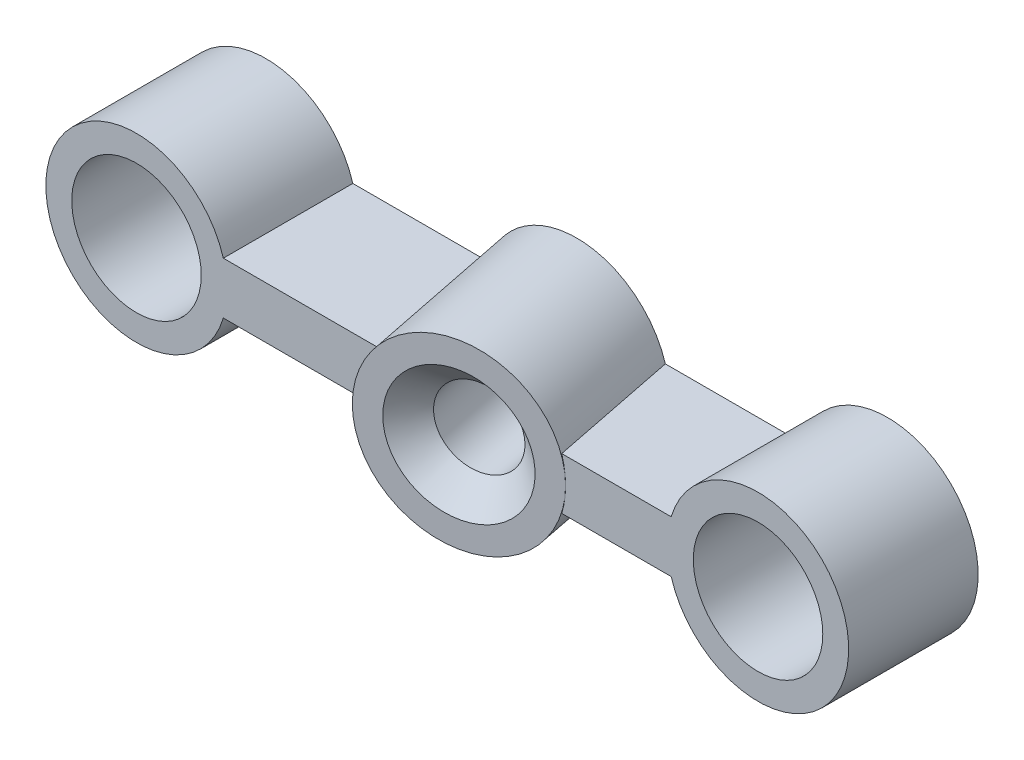
SolidWorks part; units mm, degrees
ref_plane "Front Plane" through (0, 0, 0) normal (0, 0, 1) x (1, 0, 0)
ref_plane "Top Plane" through (0, 0, 0) normal (0, 1, 0) x (1, 0, 0)
ref_plane "Right Plane" through (0, 0, 0) normal (1, 0, 0) x (0, 0, -1)
sketch "Sketch1" plane through (0, 0, 0) normal (0, 0, 1) x (1, 0, 0)
  line L0 (-20.6459, 1) -> (-3.3541, 1)
  line L1 (-3.3541, -1) -> (-20.6459, -1)
  circle A0 centre (0, 0) radius 2.5
  circle A1 centre (-24, 0) radius 2.5
  arc A2 (-20.6459, 1) -> (-20.6459, -1) centre (-24, 0) ccw
  arc A3 (-3.3541, -1) -> (-3.3541, 1) centre (0, 0) ccw
  dimension "D1" = 5
  dimension "D2" = 5
  dimension "D3" = 29
  dimension "D4" = 19
  dimension "D5" = 7
  dimension "D6" = 7
  dimension "D7" = 2
  dimension "D8" = 1
extrude "Boss-Extrude1" add sketch "Sketch1" along normal blind 5
sketch "Sketch3" plane through (0, 0, 0) normal (0, 1, 0) x (1, 0, 0)
  line L0 (0, 0) -> (0, -5) construction
  line L1 (-15.5693, 0) -> (-8.7052, 1.3728) construction
  line L2 (-3.3541, -5) -> (3.5, -5) construction
  line L3 (-3.85, 0) -> (3.85, 0) construction
  line L4 (-12.0276, 0.138) -> (-11.0507, -4.7467) construction
  line L5 (-8.7052, 1.3728) -> (-7.4307, -5)
  line L7 (-7.4307, -5) -> (-14.2948, -6.3728) construction
  line L8 (-12, 0) -> (-11, -5) construction
  line L9 (-3.3541, -5) -> (-20.6459, -5) construction
  line L10 (-14.2948, -6.3728) -> (-15.5693, 0) construction
  line L11 (-3.3541, 0) -> (-20.6459, 0) construction
  line L12 (-8.7052, 1.3728) -> (-12.1373, 0.6864)
  line L13 (-7.4307, -5) -> (-10.8627, -5.6864)
  line L14 (-10.8627, -5.6864) -> (-12.1373, 0.6864)
  point P24 (-12.1373, 0.6864)
  dimension "D1" = 7
  dimension "D4" = 12
  dimension "D5" = 11
revolve "Revolve1" add sketch "Sketch3" angle 360 about L4
sketch "Sketch4" plane through (-0.5988, 0, -2.9941) normal (-0.1961, 0, -0.9806) x (-0.9806, 0, 0.1961)
  circle A0 centre (11.767, 0) radius 1.5
  dimension "D1" = 3
extrude "Cut-Extrude1" cut sketch "Sketch4" against normal through all
sketch "Sketch5" plane through (0, 0, 0) normal (0, 1, 0) x (1, 0, 0)
  line L0 (-3.85, 0) -> (3.85, 0) construction
  line L1 (-6.8123, 0) -> (-17.4951, 0)
  line L2 (-6.8123, 0) -> (-6.8123, 3.674)
  line L3 (-6.8123, 3.674) -> (-17.4951, 3.674)
  line L4 (-17.4951, 0) -> (-17.4951, 3.674)
  point P6 (-17.4951, 0)
extrude "Cut-Extrude2" cut sketch "Sketch5" against normal through all both and the other way through all
chamfer "Chamfer1" distance 1 angle 45 1 edges at (-12.3336, 0, 5.9806)
